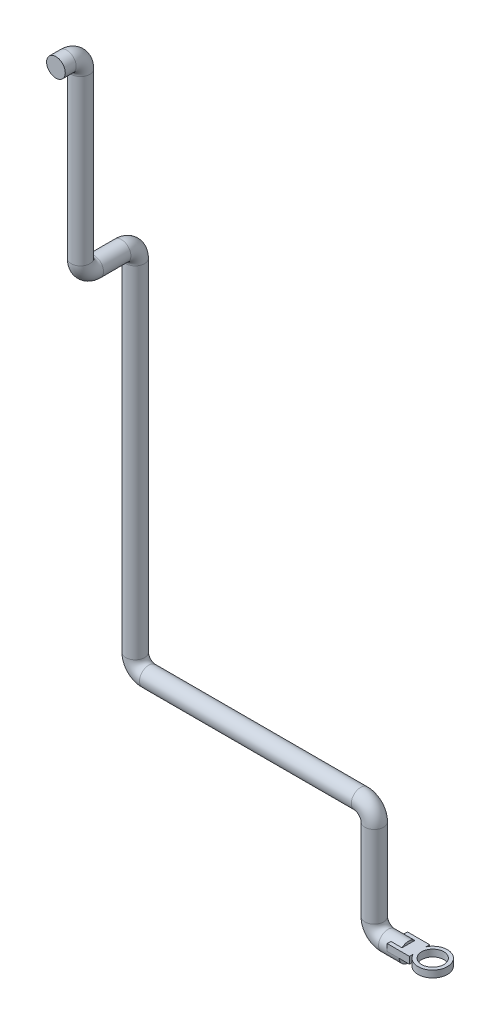
SolidWorks part; units mm, degrees
ref_plane "Alzado" through (0, 0, 0) normal (0, 0, 1) x (1, 0, 0)
ref_plane "Planta" through (0, 0, 0) normal (0, 1, 0) x (1, 0, 0)
ref_plane "Vista lateral" through (0, 0, 0) normal (1, 0, 0) x (0, 0, -1)
sketch3d "Croquis3D1"
  line L0 (0, 0, 0) -> (-30, 0, 0)
  line L1 (-50, 20, 0) -> (-50, 140, 0)
  line L2 (-70, 160, 0) -> (-380, 160, 0)
  line L3 (-400, 180, 0) -> (-400, 679.4, 0)
  line L4 (-400, 699.4, 20) -> (-400, 699.4, 60)
  line L5 (-400, 719.4, 80) -> (-400, 959.4, 80)
  line L6 (-400, 979.4, 100) -> (-400, 979.4, 116)
  arc A0 (-400, 959.4, 80) -> (-400, 979.4, 100) centre (-400, 959.4, 100) ccw
  arc A1 (-400, 699.4, 60) -> (-400, 719.4, 80) centre (-400, 719.4, 60) ccw
  arc A2 (-400, 679.4, 0) -> (-400, 699.4, 20) centre (-400, 679.4, 20) ccw
  arc A3 (-380, 160, 0) -> (-400, 180, 0) centre (-380, 180, 0) ccw
  arc A4 (-50, 140, 0) -> (-70, 160, 0) centre (-70, 140, 0) ccw
  arc A5 (-30, 0, 0) -> (-50, 20, 0) centre (-30, 20, 0) ccw
  point P12 (-400, 979.4, 80)
  point P13 (-380, 959.4, 100)
  point P16 (-400, 699.4, 80)
  point P17 (-420, 719.4, 60)
  point P20 (-400, 699.4, 0)
  point P21 (-380, 679.4, 20)
  point P24 (-400, 160, 0)
  point P25 (-380, 180, -20)
  point P28 (-50, 160, 0)
  point P29 (-70, 140, 20)
  point P32 (-50, 0, 0)
  point P33 (-30, 20, -20)
  dimension "D8" = 20
  dimension "D1" = 50
  dimension "D2" = 160
  dimension "D3" = 350
  dimension "D4" = 539.4
  dimension "D5" = 80
  dimension "D6" = 280
  dimension "D7" = 36
sketch "Croquis1" plane through (0, 0, 0) normal (1, 0, 0) x (0, 0, -1)
  circle A0 centre (0, 0) radius 13.7
  dimension "D1" = 27.4
sweep "Barrer1" add profiles "Croquis1" path "Croquis3D1"
sketch "Croquis2" plane through (0, 0, 0) normal (0, 1, 0) x (1, 0, 0)
  line L0 (0, 0) -> (35.5661, 0) construction
  line L1 (16.2659, -9.4124) -> (16.2659, -14.7869)
  line L2 (-16.2659, 14.7869) -> (16.2659, 14.7869)
  line L3 (-16.2659, 14.7869) -> (-16.2659, -14.7869)
  line L4 (-16.2659, -14.7869) -> (16.2659, -14.7869)
  line L5 (16.2659, 14.7869) -> (16.2659, 9.4124)
  line L6 (-16.2659, 14.7869) -> (16.2659, -14.7869) construction
  line L7 (-16.2659, -14.7869) -> (16.2659, 14.7869) construction
  circle A0 centre (35.5661, 0) radius 21.473
  circle A1 centre (35.5661, 0) radius 16.2373
extrude "Saliente-Extruir1" add sketch "Croquis2" along normal blind 10 contours A0 L5 L2 L3 L4 L1 | A0 A1
